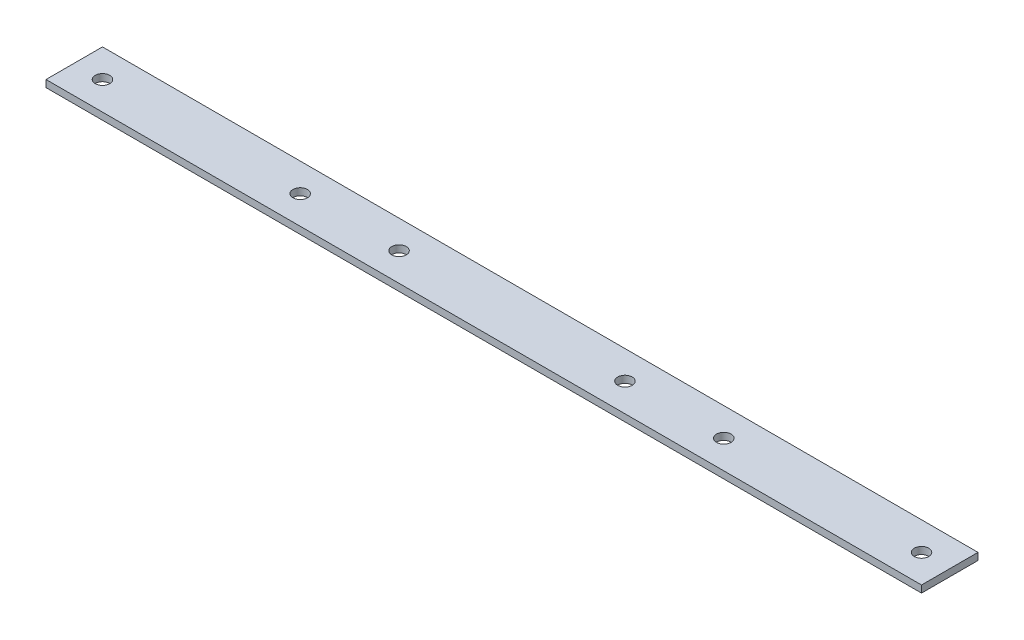
SolidWorks part; units mm, degrees
material "Alloy Steel"
ref_plane "Front Plane" through (0, 0, 0) normal (0, 0, 1) x (1, 0, 0)
ref_plane "Top Plane" through (0, 0, 0) normal (0, 1, 0) x (1, 0, 0)
ref_plane "Right Plane" through (0, 0, 0) normal (1, 0, 0) x (0, 0, -1)
sketch "Sketch1" plane through (0, 0, 0) normal (0, 1, 0) x (1, 0, 0)
  line L1 (-196.85, -12.7) -> (196.85, -12.7)
  line L2 (-196.85, -12.7) -> (-196.85, 12.7)
  line L3 (-196.85, 12.7) -> (196.85, 12.7)
  line L4 (196.85, -12.7) -> (196.85, 12.7)
  line L5 (-196.85, -12.7) -> (196.85, 12.7) construction
  line L6 (-196.85, 12.7) -> (196.85, -12.7) construction
  point P0 (0, 0)
  dimension "D1" = 25.4
  dimension "D2" = 393.7
extrude "Boss-Extrude1" add sketch "Sketch1" along normal mid plane 3.175
sketch "Sketch2" plane through (0, 1.5875, 0) normal (0, 1, 0) x (1, 0, 0)
  line L0 (-165.1, 12.7) -> (-165.1, -12.7) construction
  line L1 (196.85, 12.7) -> (-196.85, 12.7) construction
  line L2 (-196.85, -12.7) -> (196.85, -12.7) construction
  line L3 (-139.7, 12.7) -> (-139.7, -12.7) construction
  line L4 (165.1, 12.7) -> (165.1, -12.7) construction
  line L5 (-196.85, 12.7) -> (-196.85, -12.7) construction
  line L6 (139.7, 12.7) -> (139.7, -12.7) construction
  line L7 (196.85, -12.7) -> (196.85, 12.7) construction
  line L9 (-184.15, 0) -> (184.15, 0) construction
  circle A0 centre (-184.15, 0) radius 3.2639
  circle A1 centre (184.15, 0) radius 3.2639
  circle A2 centre (-95.25, 0) radius 3.2639
  circle A3 centre (95.25, 0) radius 3.2639
  circle A4 centre (-50.8, 0) radius 3.2639
  circle A5 centre (50.8, 0) radius 3.2639
  dimension "D5" = 6.5278
  dimension "D6" = 44.45
  dimension "D7" = 44.45
  dimension "D8" = 44.45
  dimension "D9" = 44.45
  dimension "D10" = 12.7
  dimension "D11" = 12.7
  dimension "D1" = 31.75
  dimension "D2" = 25.4
  dimension "D3" = 31.75
  dimension "D4" = 25.4
extrude "Cut-Extrude1" cut sketch "Sketch2" against normal through all both
